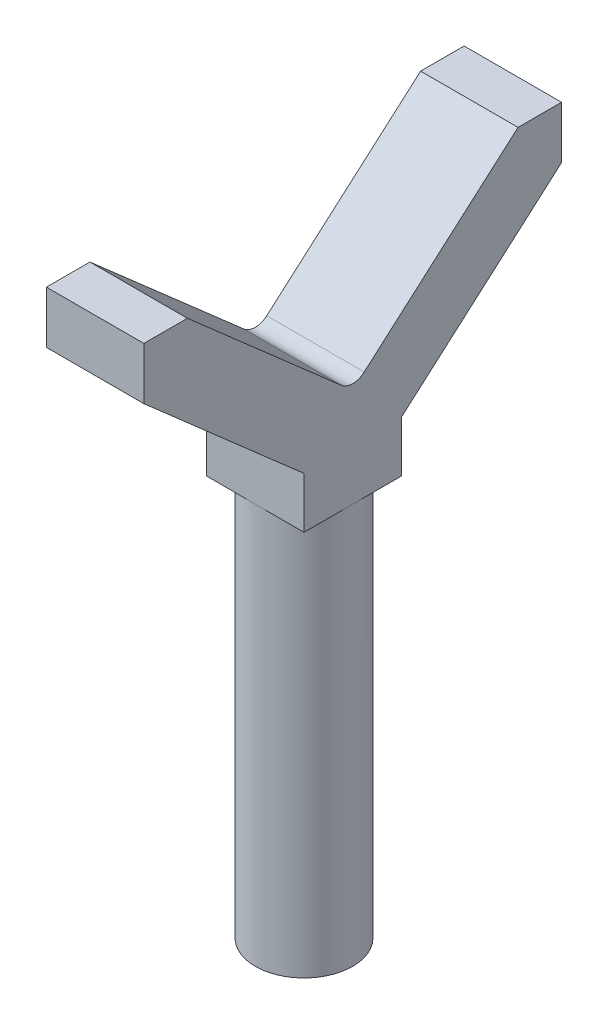
SolidWorks part; units mm, degrees
ref_plane "Front Plane" through (0, 0, 0) normal (0, 0, 1) x (1, 0, 0)
ref_plane "Top Plane" through (0, 0, 0) normal (0, 1, 0) x (1, 0, 0)
ref_plane "Right Plane" through (0, 0, 0) normal (1, 0, 0) x (0, 0, -1)
sketch "Sketch1" plane through (0, 0, 0) normal (0, 1, 0) x (1, 0, 0)
  circle A0 centre (0, 0) radius 28
  dimension "D1" = 56
extrude "Boss-Extrude1" add sketch "Sketch1" along normal blind 230
sketch "Sketch2" plane through (0, 0, 0) normal (1, 0, 0) x (0, 0, -1)
  line L0 (0, 290) -> (0, -49.5362) construction
  line L1 (6.5929, 292.4811) -> (95, 370)
  line L2 (95, 370) -> (120, 370)
  line L3 (120, 370) -> (120, 340)
  line L4 (120, 340) -> (28, 259.3307)
  line L5 (28, 259.3307) -> (28, 230)
  line L8 (28, 230) -> (-28, 230)
  line L9 (-120, 340) -> (-28, 259.3307)
  line L10 (-120, 370) -> (-120, 340)
  line L11 (-95, 370) -> (-120, 370)
  line L12 (-6.5929, 292.4811) -> (-95, 370)
  line L14 (-28, 230) -> (-28, 259.3307)
  arc A0 (-6.5929, 292.4811) -> (6.5929, 292.4811) centre (0, 300) ccw
  point P5 (0, 304.0365)
  dimension "D3" = 10
  dimension "D1" = 30
  dimension "D2" = 240
  dimension "D4" = 190
  dimension "D5" = 370
  dimension "D6" = 80
extrude "Boss-Extrude2" add sketch "Sketch2" along normal mid plane 56
